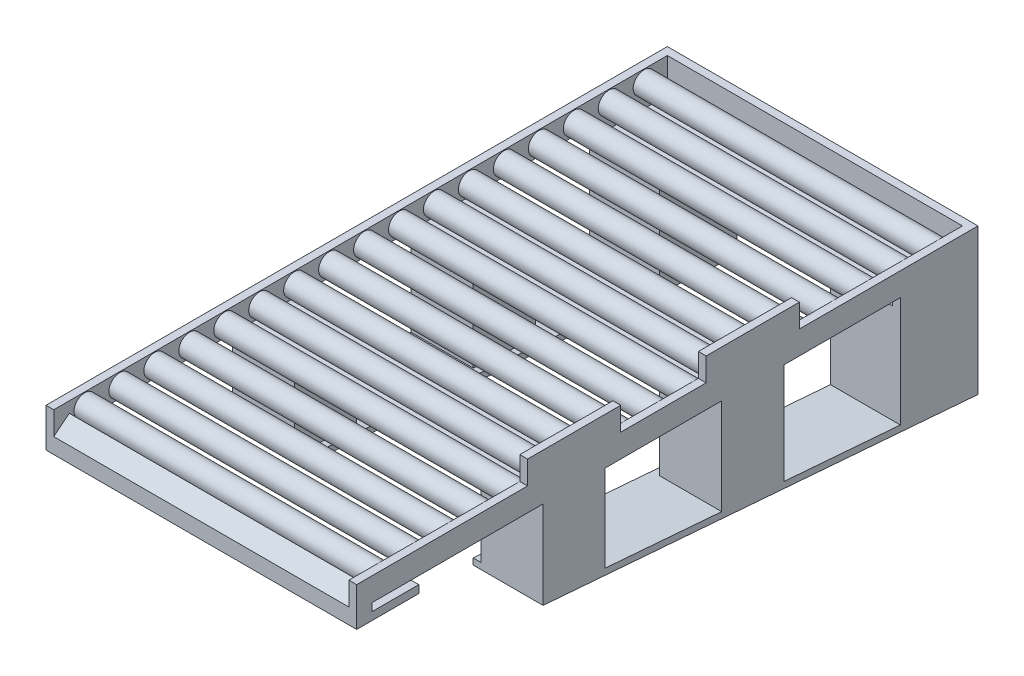
SolidWorks part; units mm, degrees
ref_plane "Front Plane" through (0, 0, 0) normal (0, 0, 1) x (1, 0, 0)
ref_plane "Top Plane" through (0, 0, 0) normal (0, 1, 0) x (1, 0, 0)
ref_plane "Right Plane" through (0, 0, 0) normal (1, 0, 0) x (0, 0, -1)
sketch "Sketch2" plane through (0, 0, 0) normal (0, 1, 0) x (1, 0, 0)
  line L0 (-1900, -3900) -> (-1900, 3900)
  line L1 (-2000, -4000) -> (2000, -4000)
  line L2 (-2000, -4000) -> (-2000, 4000)
  line L3 (-2000, 4000) -> (2000, 4000)
  line L4 (2000, -4000) -> (2000, 4000)
  line L5 (-2000, -4000) -> (2000, 4000) construction
  line L6 (-2000, 4000) -> (2000, -4000) construction
  line L7 (-1900, 3900) -> (1900, 3900)
  line L8 (1900, -3900) -> (1900, 3900)
  line L9 (-1900, -3900) -> (1900, -3900)
  point P0 (0, 0)
  dimension "D1" = 8000
  dimension "D2" = 4000
  dimension "D3" = 100
extrude "Boss-Extrude1" add sketch "Sketch2" along normal blind 300
sketch "Sketch3" plane through (-1900, 0, 0) normal (1, 0, 0) x (0, 0, -1)
  line L0 (4000, 300) -> (4000, 0) construction
  circle A0 centre (3600, 150) radius 140
  point P2 (0, 0)
  point P5 (4000, 150)
  dimension "D1" = 280
  dimension "D2" = 400
extrude "Boss-Extrude2" add sketch "Sketch3" along normal up to surface (3800 mm away) up to face at (1900, 150, 0)
pattern_linear "LPattern1" count 17 spacing 450 along (0, 0, 1) of "Boss-Extrude2"
sketch "Sketch4" plane through (0, 0, 0) normal (0, -1, 0) x (1, 0, 0)
  line L0 (-1900, -3000) -> (-2000, -3000)
  line L1 (-1900, -3900) -> (-1900, 3900) construction
  line L2 (-2000, -4000) -> (-2000, 4000) construction
  line L3 (-2000, -3000) -> (-2000, -4000)
  line L4 (2000, -4000) -> (-2000, -4000)
  line L5 (2000, -4000) -> (2000, -3000)
  line L6 (2000, 4000) -> (2000, -4000) construction
  line L7 (1900, -3000) -> (2000, -3000)
  line L8 (1900, -3000) -> (1900, -3900)
  line L9 (1900, 3900) -> (1900, -3900) construction
  line L10 (1900, -3900) -> (-1900, -3900)
  line L11 (-1900, -3900) -> (-1900, -3000)
  dimension "D1" = 1000
  dimension "D2" = 1000
extrude "Boss-Extrude3" add sketch "Sketch4" along normal blind 200
sketch "Sketch5" plane through (0, -200, 0) normal (0, -1, 0) x (1, 0, 0)
  line L1 (2000, -4000) -> (-2000, -4000)
  line L2 (2000, -4000) -> (2000, -3000)
  line L3 (2000, -3000) -> (-2000, -3000)
  line L4 (-2000, -4000) -> (-2000, -3000)
extrude "Boss-Extrude4" add sketch "Sketch5" against normal blind 57
sketch "Sketch6" plane through (0, 0, 0) normal (0, -1, 0) x (-1, 0, 0)
  line L0 (-2000, -4000) -> (-2000, 3000) construction
  line L1 (2000, -4000) -> (-2000, -4000)
  line L2 (2000, -4000) -> (2000, -3200)
  line L3 (2000, -3200) -> (-2000, -3200)
  line L4 (-2000, -4000) -> (-2000, -3200)
  dimension "D1" = 800
extrude "Boss-Extrude5" add sketch "Sketch6" along normal blind 200
sketch "Sketch7" plane through (0, 0, 0) normal (0, -1, 0) x (-1, 0, 0)
  line L0 (2000, 3000) -> (2000, -3200) construction
  line L1 (2000, 1500) -> (-2000, 1500)
  line L2 (2000, 1500) -> (2000, 700)
  line L3 (2000, 700) -> (-2000, 700)
  line L4 (-2000, 1500) -> (-2000, 700)
  line L5 (-2000, -3200) -> (-2000, 3000) construction
  point P8 (0, 700)
  dimension "D1" = 800
  dimension "D2" = 700
extrude "Boss-Extrude6" add sketch "Sketch7" along normal blind 200
sketch "Sketch8" plane through (0, 0, 0) normal (0, -1, 0) x (-1, 0, 0)
  line L0 (-2000, -3200) -> (-2000, 700) construction
  line L1 (-2000, -1600) -> (2000, -1600)
  line L2 (-2000, -1600) -> (-2000, -800)
  line L3 (-2000, -800) -> (2000, -800)
  line L4 (2000, -1600) -> (2000, -800)
  line L5 (2000, 700) -> (2000, -3200) construction
  point P8 (0, -800)
  dimension "D1" = 800
  dimension "D2" = 800
extrude "Boss-Extrude7" add sketch "Sketch8" along normal blind 200
sketch "Sketch9" plane through (0, 0, 3900) normal (0, 0, -1) x (-1, 0, 0)
  line L1 (1900, 0) -> (-1900, 0)
  line L2 (1900, 0) -> (1900, 300)
  line L3 (1900, 300) -> (-1900, 300)
  line L4 (-1900, 0) -> (-1900, 300)
extrude "Cut-Extrude1" cut sketch "Sketch9" against normal blind 200
sketch "Sketch10" plane through (-1900, 0, 0) normal (1, 0, 0) x (0, 0, -1)
  line L0 (-4000, 0) -> (-3800, 160)
  line L1 (-3800, 160) -> (-3800, 0)
  line L2 (-4000, 0) -> (-3200, 0) construction
  line L3 (-3800, 0) -> (-4000, 0)
  dimension "D1" = 200
  dimension "D2" = 160
extrude "Boss-Extrude8" add sketch "Sketch10" along normal up to surface (3800 mm away) up to face at (1900, 150, 3740)
sketch "Sketch11" plane through (2000, 0, 0) normal (1, 0, 0) x (0, 0, -1)
  line L0 (500, 300) -> (500, 600)
  line L1 (-4000, 300) -> (4000, 300) construction
  line L2 (500, 600) -> (1700, 600)
  line L3 (-800, -200) -> (-1600, -200) construction
  line L4 (1700, 600) -> (1700, 300)
  line L5 (1500, -200) -> (700, -200) construction
  line L6 (500, 300) -> (1700, 300)
  line L7 (-1800, 300) -> (-600, 300)
  line L8 (-600, 600) -> (-1800, 600)
  line L9 (-600, 300) -> (-600, 600)
  line L10 (-1800, 600) -> (-1800, 300)
  point P4 (1100, 600)
  point P9 (1100, -200)
  point P10 (-1200, 600)
  point P18 (-1200, -200)
  dimension "D1" = 300
  dimension "D2" = 1200
  dimension "D3" = 300
  dimension "D4" = 1200
  dimension "D5" = 500
extrude "Boss-Extrude9" add sketch "Sketch11" against normal up to surface (100 mm away) up to face at (1900, 150, 3740)
sketch "Sketch12" plane through (0, -200, 0) normal (0, -1, 0) x (1, 0, 0)
  line L0 (2000, -3000) -> (-2000, -3000) construction
  line L1 (-2000, -4000) -> (-1100, -4000)
  line L2 (-2000, -4000) -> (-2000, -3000)
  line L3 (-2000, -3000) -> (-1100, -3000)
  line L4 (-1100, -4000) -> (-1100, -3000)
  line L5 (-2000, -4000) -> (2000, -4000) construction
  line L6 (2000, -3000) -> (1100, -3000)
  line L7 (2000, -3000) -> (2000, -4000)
  line L8 (2000, -4000) -> (1100, -4000)
  line L9 (1100, -3000) -> (1100, -4000)
  dimension "D1" = 900
  dimension "D2" = 900
extrude "Boss-Extrude10" add sketch "Sketch12" along normal blind 1300
sketch "Sketch13" plane through (0, -200, 0) normal (0, -1, 0) x (1, 0, 0)
  line L0 (2000, -700) -> (-2000, -700) construction
  line L1 (-2000, -1500) -> (-1200, -1500)
  line L2 (-2000, -1500) -> (-2000, -700)
  line L3 (-2000, -700) -> (-1200, -700)
  line L4 (-1200, -1500) -> (-1200, -700)
  line L5 (-2000, -1500) -> (2000, -1500) construction
  line L6 (2000, -700) -> (1200, -700)
  line L7 (2000, -700) -> (2000, -1500)
  line L8 (2000, -1500) -> (1200, -1500)
  line L9 (1200, -700) -> (1200, -1500)
  dimension "D1" = 800
  dimension "D2" = 800
extrude "Boss-Extrude11" add sketch "Sketch13" along normal blind 1100
sketch "Sketch14" plane through (2000, 0, 0) normal (1, 0, 0) x (0, 0, -1)
  line L0 (700, -1300) -> (1500, -1380)
  line L1 (1500, -1300) -> (1500, -1380)
  line L28 (3000, 0) -> (3000, -1500)
  line L29 (3000, -1500) -> (4000, -1500)
  line L30 (4000, -1500) -> (4000, 300)
  line L31 (4000, 300) -> (1700, 300)
  line L32 (1700, 300) -> (1700, 600)
  line L33 (1700, 600) -> (500, 600)
  line L34 (500, 600) -> (500, 300)
  line L35 (500, 300) -> (-600, 300)
  line L36 (-600, 300) -> (-600, 600)
  line L37 (-600, 600) -> (-1800, 600)
  line L38 (-1800, 600) -> (-1800, 300)
  line L39 (-1800, 300) -> (-4000, 300)
  line L40 (-4000, 300) -> (-4000, -200)
  line L41 (-4000, -200) -> (-3200, -200)
  line L42 (-3200, -200) -> (-3200, 0)
  line L43 (-3200, 0) -> (-1600, 0)
  line L44 (-1600, 0) -> (-1600, -200)
  line L45 (-1600, -200) -> (-800, -200)
  line L46 (-800, -200) -> (-800, 0)
  line L47 (-800, 0) -> (700, 0)
  line L48 (700, 0) -> (700, -1300)
  line L49 (700, -1300) -> (1500, -1300)
  line L50 (1500, -1300) -> (1500, 0)
  line L51 (1500, 0) -> (3000, 0)
  line L73 (700, -1300) -> (1500, -1300)
  point P6 (1500, -1390.3547)
  dimension "D1" = 80
  dimension "D2" = 0
extrude "Boss-Extrude12" add sketch "Sketch14" against normal blind 800
sketch "Sketch16" plane through (2000, 0, 0) normal (1, 0, 0) x (0, 0, -1)
  line L0 (3000, -1500) -> (4000, -1580)
  line L1 (4000, -1500) -> (4000, -1580)
  line L26 (3000, 0) -> (3000, -1500)
  line L27 (3000, -1500) -> (4000, -1500)
  line L28 (4000, -1500) -> (4000, 300)
  line L29 (4000, 300) -> (1700, 300)
  line L30 (1700, 300) -> (1700, 600)
  line L31 (1700, 600) -> (500, 600)
  line L32 (500, 600) -> (500, 300)
  line L33 (500, 300) -> (-600, 300)
  line L34 (-600, 300) -> (-600, 600)
  line L35 (-600, 600) -> (-1800, 600)
  line L36 (-1800, 600) -> (-1800, 300)
  line L37 (-1800, 300) -> (-4000, 300)
  line L38 (-4000, 300) -> (-4000, -200)
  line L39 (-4000, -200) -> (-3200, -200)
  line L40 (-3200, -200) -> (-3200, 0)
  line L41 (-3200, 0) -> (-1600, 0)
  line L42 (-1600, 0) -> (-1600, -200)
  line L43 (-1600, -200) -> (-800, -200)
  line L44 (-800, -200) -> (-800, 0)
  line L45 (-800, 0) -> (700, 0)
  line L46 (700, 0) -> (700, -1300)
  line L47 (700, -1300) -> (1500, -1380)
  line L48 (1500, -1380) -> (1500, 0)
  line L49 (1500, 0) -> (3000, 0)
  line L51 (3000, -1500) -> (4000, -1500)
  dimension "D1" = 80
  dimension "D2" = 0
extrude "Boss-Extrude13" add sketch "Sketch16" against normal blind 900 separate body
ref_plane "Plane1" through (0, -1261.9554, 100.9564) normal (0, -0.9968, 0.0797) x (-1, 0, 0)
sketch "Sketch20" plane through (0, -200, 0) normal (0, -1, 0) x (1, 0, 0)
  line L1 (-2000, 800) -> (-1200, 800)
  line L2 (-2000, 800) -> (-2000, 1600)
  line L3 (-2000, 1600) -> (-1200, 1600)
  line L4 (-1200, 800) -> (-1200, 1600)
  dimension "D1" = 800
  dimension "D2" = 800
sketch "Sketch21" plane through (-2000, 0, 0) normal (-1, 0, 0) x (0, 0, 1)
  line L0 (-4000, -1500) -> (-4000, -1580)
  line L1 (-4000, -1580) -> (-3000, -1500)
  line L2 (-4000, -1500) -> (-3000, -1500)
extrude "Boss-Extrude15" add sketch "Sketch21" against normal blind 4000
sketch "Sketch24" plane through (2000, 0, 0) normal (1, 0, 0) x (0, 0, -1)
  line L0 (700, -1300) -> (1500, -1300)
  line L1 (1500, -1300) -> (1500, -1380)
  line L2 (1500, -1380) -> (700, -1300)
  point P3 (0, 0)
  point P6 (1554.7294, -1300)
  point P7 (1500, -1300)
extrude "Cut-Extrude3" cut sketch "Sketch24" against normal through all
sketch "Sketch27" plane through (0, 0, 0) normal (1, 0, 0) x (0, 0, -1)
  line L0 (4000, -1580) -> (-4000, -940)
  line L2 (3000, -1500) -> (4000, -1580) construction
  line L3 (-4000, -940) -> (-4000, -860)
  line L4 (-4000, -860) -> (4000, -1500)
  line L5 (4000, -1500) -> (4000, -1580)
extrude "Boss-Extrude16" add sketch "Sketch27" along normal up to surface and the other way up to surface
extrude "Boss-Extrude17" add sketch "Sketch20" along normal up to surface (916 mm away)
sketch "Sketch28" plane through (0, -200, 0) normal (0, -1, 0) x (1, 0, 0)
  line L1 (2000, 1600) -> (1200, 1600)
  line L2 (2000, 1600) -> (2000, 800)
  line L3 (2000, 800) -> (1200, 800)
  line L4 (1200, 1600) -> (1200, 800)
  dimension "D1" = 800
  dimension "D2" = 800
extrude "Boss-Extrude18" add sketch "Sketch28" along normal up to surface (852 mm away)
sketch "Sketch29" plane through (0, 0, 0) normal (0, 0, 1) x (1, 0, 0)
  line L0 (-1100, -1500) -> (-1100, -200) construction
  line L1 (1100, -2125.7405) -> (-1100, -2125.7405)
  line L2 (1100, -2125.7405) -> (1100, -379.8042)
  line L3 (1100, -379.8042) -> (-1100, -379.8042)
  line L4 (-1100, -2125.7405) -> (-1100, -379.8042)
extrude "Cut-Extrude4" cut sketch "Sketch29" along normal through all and the other way blind 4000
sketch "Sketch30" plane through (0, 0, 0) normal (1, 0, 0) x (0, 0, -1)
  line L1 (-1600, -2172.4092) -> (-4059.6721, -2172.4092)
  line L2 (-1600, -2172.4092) -> (-1600, -388.1078)
  line L3 (-1600, -388.1078) -> (-4059.6721, -388.1078)
  line L4 (-4059.6721, -2172.4092) -> (-4059.6721, -388.1078)
extrude "Cut-Extrude5" cut sketch "Sketch30" against normal mid plane 4000
sketch "Sketch31" plane through (-2000, 0, 0) normal (-1, 0, 0) x (0, 0, 1)
  line L1 (3802.1589, -100) -> (3200, -100)
  line L2 (3802.1589, -100) -> (3802.1589, 0)
  line L3 (3802.1589, 0) -> (3200, 0)
  line L4 (3200, -100) -> (3200, 0)
  point P5 (3802.1589, -142.384)
  point P6 (3802.1589, -50)
  dimension "D1" = 50
  dimension "D2" = 602.1589
extrude "Cut-Extrude6" cut sketch "Sketch31" against normal blind 4000
